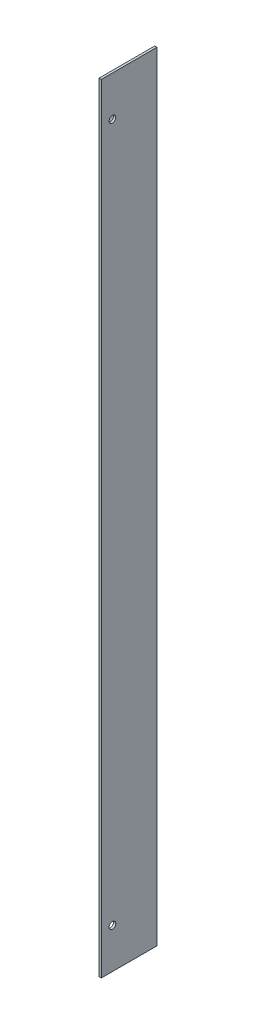
SolidWorks part; units mm, degrees
material "Plástico personalizado"
ref_plane "Alzado" through (0, 0, 0) normal (0, 0, 1) x (1, 0, 0)
ref_plane "Planta" through (0, 0, 0) normal (0, 1, 0) x (1, 0, 0)
ref_plane "Vista lateral" through (0, 0, 0) normal (1, 0, 0) x (0, 0, -1)
sketch "Croquis1" plane through (0, 0, 0) normal (0, 0, 1) x (1, 0, 0)
  line L0 (-55.4418, 61.1804) -> (-79.4418, 37.1804)
  line L1 (-79.4418, -264.8196) -> (-79.4418, 37.1804)
  line L4 (-55.4418, 61.1804) -> (-55.4418, -288.8196)
  line L5 (-55.4418, -288.8196) -> (-79.4418, -264.8196)
  circle A0 centre (-74.4418, 1.1804) radius 1.5
  circle A1 centre (-74.4418, -228.8196) radius 1.5
  dimension "D1" = 5
  dimension "D4" = 24
  dimension "D2" = 350
  dimension "D3" = 5
  dimension "D5" = 60
  dimension "D6" = 60
  dimension "D7" = 45
  dimension "D8" = 45
sketch "Croquis2" plane through (0, 0, 0) normal (0, 0, 1) x (1, 0, 0)
  line L1 (-55.4418, 61.1804) -> (-54.4418, 61.1804)
  line L2 (-55.4418, 61.1804) -> (-55.4418, -288.8196)
  line L3 (-55.4418, -288.8196) -> (-54.4418, -288.8196)
  line L4 (-54.4418, 61.1804) -> (-54.4418, -288.8196)
  dimension "D1" = 1
  dimension "D2" = 350
extrude "Saliente-Extruir2" add sketch "Croquis2" along normal blind 25
sketch "Croquis5" plane through (-54.4418, 0, 0) normal (1, 0, 0) x (0, 0, -1)
  line L0 (-25, 61.1804) -> (0, 61.1804) construction
  line L1 (-25, -288.8196) -> (0, -288.8196) construction
  line L2 (-25, -288.8196) -> (-25, 61.1804) construction
  circle A0 centre (-20, 43.1804) radius 1.5
  circle A1 centre (-20, -270.8196) radius 1.5
  dimension "D1" = 18
  dimension "D4" = 5
  dimension "D2" = 18
  dimension "D3" = 5
extrude "Cortar-Extruir2" cut sketch "Croquis5" against normal blind 1
extrude "Saliente-Extruir3" add sketch "Croquis1" along normal blind 1
